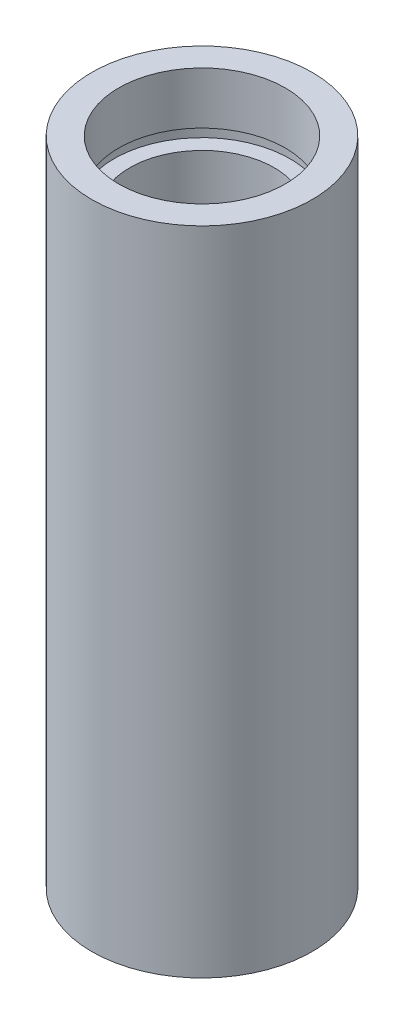
SolidWorks part; units mm, degrees
ref_plane "前视基准面" through (0, 0, 0) normal (0, 0, 1) x (1, 0, 0)
ref_plane "上视基准面" through (0, 0, 0) normal (0, 1, 0) x (1, 0, 0)
ref_plane "右视基准面" through (0, 0, 0) normal (1, 0, 0) x (0, 0, -1)
sketch "草图1" plane through (0, 0, 0) normal (0, 0, 1) x (1, 0, 0)
  line L0 (0, 161.3762) -> (0, 0) construction
  line L1 (141.7365, 0) -> (-131.7984, 0) construction
  line L2 (7, 0) -> (7, 4.5)
  line L3 (7.6, 4.5) -> (7.6, 5.5)
  line L4 (7, 4.5) -> (7.6, 4.5)
  line L5 (6.25, 5.5) -> (6.25, 50.8)
  line L6 (6.25, 5.5) -> (7.6, 5.5)
  line L7 (7.6, 50.8) -> (7.6, 51.8)
  line L8 (6.25, 50.8) -> (7.6, 50.8)
  line L9 (7.2, 51.8) -> (7.2, 56.3)
  line L10 (7.2, 51.8) -> (7.6, 51.8)
  line L11 (9.525, 0) -> (9.525, 56.3)
  line L12 (7, 0) -> (9.525, 0)
  line L13 (7.2, 56.3) -> (9.525, 56.3)
  dimension "D1" = 7
  dimension "D2" = 4.5
  dimension "D3" = 7.6
  dimension "D4" = 6.25
  dimension "D5" = 1
  dimension "D6" = 1
  dimension "D7" = 7.2
  dimension "D8" = 4.5
  dimension "D9" = 9.525
  dimension "D10" = 50.8
revolve "旋转1" add sketch "草图1" angle 360 about L0
cosmetic thread "装饰螺纹线1" parameters "D2"=15
cosmetic thread "装饰螺纹线2" parameters "D2"=13.5
cosmetic thread "装饰螺纹线3" parameters "D2"=15.01
